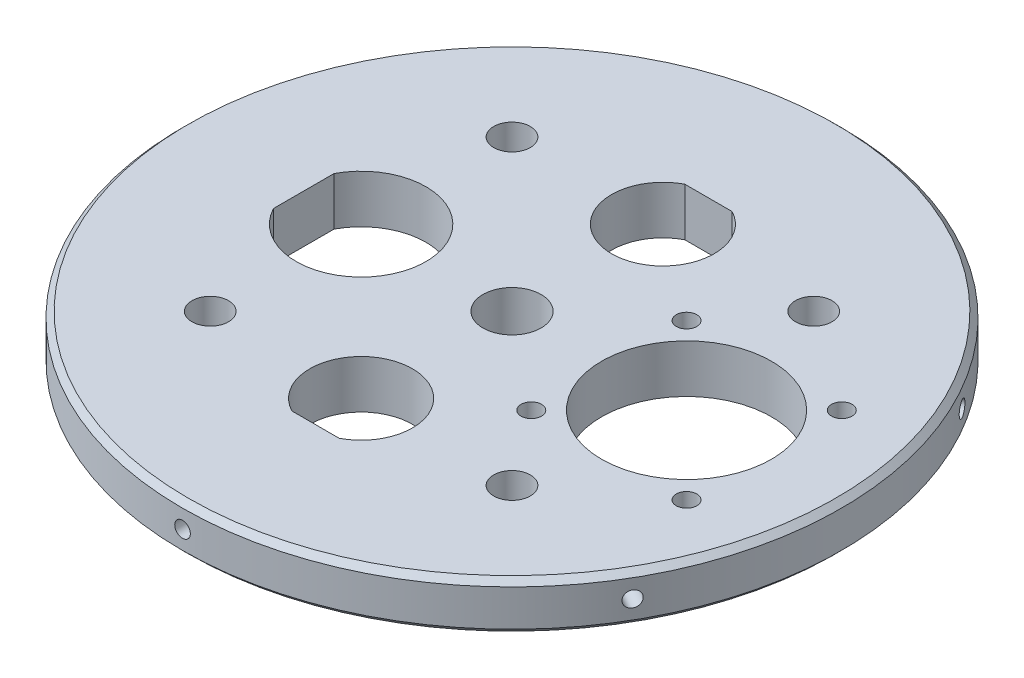
SolidWorks part; units mm, degrees
ref_plane "Front Plane" through (0, 0, 0) normal (0, 0, 1) x (1, 0, 0)
ref_plane "Top Plane" through (0, 0, 0) normal (0, 1, 0) x (1, 0, 0)
ref_plane "Right Plane" through (0, 0, 0) normal (1, 0, 0) x (0, 0, -1)
sketch "Sketch2" plane through (0, 0, 0) normal (0, 1, 0) x (1, 0, 0)
  circle A0 centre (0, 0) radius 57.15
  dimension "D1" = 114.3
extrude "Boss-Extrude1" add sketch "Sketch2" along normal blind 8.35 contours A0
sketch "Sketch6" plane through (0, 8.35, 0) normal (0, 1, 0) x (1, 0, 0)
  circle A0 centre (-26.1629, -26.1629) radius 3.175
  circle A1 centre (26.1629, -26.1629) radius 3.175
  circle A2 centre (-26.1629, 26.1631) radius 3.175
  circle A3 centre (26.1629, 26.1631) radius 3.175
  dimension "D1" = 6.35
  dimension "D2" = 74
  dimension "D3" = 26.1629
  dimension "D4" = 26.1629
  dimension "D5" = 26.1629
extrude "Cut-Extrude1" cut sketch "Sketch6" against normal up to next
sketch "Sketch7" plane through (0, 8.35, 0) normal (0, 1, 0) x (1, 0, 0)
  circle A0 centre (30, 0.2699) radius 14.732
  circle A3 centre (16.54, -13.1941) radius 1.778
  circle A4 centre (16.54, 13.7299) radius 1.778
  circle A5 centre (43.46, 13.7299) radius 1.778
  circle A6 centre (43.46, -13.1941) radius 1.778
  dimension "D1" = 29.464
  dimension "D2" = 3.556
  dimension "D3" = 3.556
  dimension "D4" = 3.556
  dimension "D5" = 3.556
  dimension "D6" = 13.46
  dimension "D7" = 13.46
  dimension "D8" = 13.46
  dimension "D9" = 13.464
  dimension "D10" = 30
extrude "Cut-Extrude2" cut sketch "Sketch7" against normal through all
sketch "Sketch8" plane through (0, 8.35, 0) normal (0, 1, 0) x (1, 0, 0)
  line L0 (4.0988, 34.0631) -> (-4.0988, 34.0631)
  line L1 (4.0988, -34.0629) -> (-4.0988, -34.0629)
  line L2 (-36.1129, 5.2498) -> (-36.1129, -5.2498)
  arc A0 (4.0988, -34.0629) -> (-4.0988, -34.0629) centre (0, -26.1629) ccw
  arc A1 (-4.0988, 34.0631) -> (4.0988, 34.0631) centre (0, 26.1631) ccw
  circle A2 centre (0, 0) radius 5.042
  arc A3 (-36.1129, -5.2498) -> (-36.1129, 5.2498) centre (-26.1629, 0) ccw
  circle A4 centre (26.1629, -26.1629) radius 3.175 construction
  circle A5 centre (26.1629, 26.1631) radius 3.175 construction
  circle A6 centre (-26.1629, -26.1629) radius 3.175 construction
  dimension "D1" = 17.8
  dimension "D2" = 17.8
  dimension "D3" = 10.084
  dimension "D4" = 22.5
  dimension "D5" = 7.9
  dimension "D6" = 0
  dimension "D7" = 7.9
  dimension "D8" = 0
  dimension "D9" = 9.95
  dimension "D10" = 0
extrude "Cut-Extrude3" cut sketch "Sketch8" against normal through all
sketch "Sketch10" plane through (0, 8.35, 0) normal (0, 1, 0) x (1, 0, 0)
  circle A0 centre (-26.1629, 26.1631) radius 7.9375
  circle A1 centre (26.1631, 26.1629) radius 7.9375
  circle A2 centre (26.1629, -26.1631) radius 7.9375
  circle A3 centre (-26.1631, -26.1629) radius 7.9375
  point P11 (0, 0)
  dimension "D1" = 4
sketch "Sketch11" plane through (0, 8.35, 0) normal (0, 1, 0) x (1, 0, 0)
  circle A0 centre (0, 0) radius 10
ref_plane "Plane1" through (0, 0, -57.15) normal (0, 0, -1) x (-1, 0, 0)
sketch "Sketch12" plane through (0, 0, -57.15) normal (0, 0, -1) x (-1, 0, 0)
  line L0 (57.15, 0) -> (57.15, 8.35) construction
  point P0 (0, 4.175)
  point P1 (57.15, 4.175)
hole_wizard "#6-32 Tapped Hole1" positions "3DSketch7" profile "Sketch16" tap size "#6-32" standard "ANSI Inch"
sketch3d "3DSketch7"
  point P0 (0, 4.175, -57.15)
cosmetic thread "Hole Thread2" parameters "D1"=12.7, "D2"=3.5052
sketch "Sketch16" plane through (0, 4.175, -57.15) normal (1, 0, 0) x (0, 1, 0)
  line L0 (0, 0) -> (0, 13.8127)
  line L1 (0, 13.8127) -> (1.3525, 13)
  line L2 (1.3525, 13) -> (1.3525, 0)
  line L5 (1.3525, 0) -> (0, 0)
  line L10 (0, 13.8127) -> (-1.3526, 13) construction
  line L11 (0, -6.35) -> (0, 107.95) construction
  dimension "Tap Drill Dia." = 2.7051
  dimension "Tap Drill Depth" = 13
  dimension "Drill Angle" = 118
pattern_circular "CirPattern1" count 6 over 360 about axis through (0, 0, 0) along (0, 1, 0) of "#6-32 Tapped Hole1"
cosmetic thread "Hole Thread3" parameters "D1"=12.7, "D2"=3.5052
cosmetic thread "Hole Thread4" parameters "D1"=12.7, "D2"=3.5052
cosmetic thread "Hole Thread5" parameters "D1"=12.7, "D2"=3.5052
cosmetic thread "Hole Thread6" parameters "D1"=12.7, "D2"=3.5052
cosmetic thread "Hole Thread7" parameters "D1"=12.7, "D2"=3.5052
cosmetic thread "Hole Thread8" parameters "D1"=12.7, "D2"=3.5052
cosmetic thread "Hole Thread9" parameters "D1"=12.7, "D2"=3.5052
chamfer "Chamfer1" distance 1 angle 45 2 edges at (0, 8.35, 57.15) (0, 0, 57.15)
equation "\"width\"=26.1629"
equation "\"D4@Sketch6\"=\"width\""
equation "\"D3@Sketch6\"=\"width\""
equation "\"D5@Sketch6\"=\"width\""
